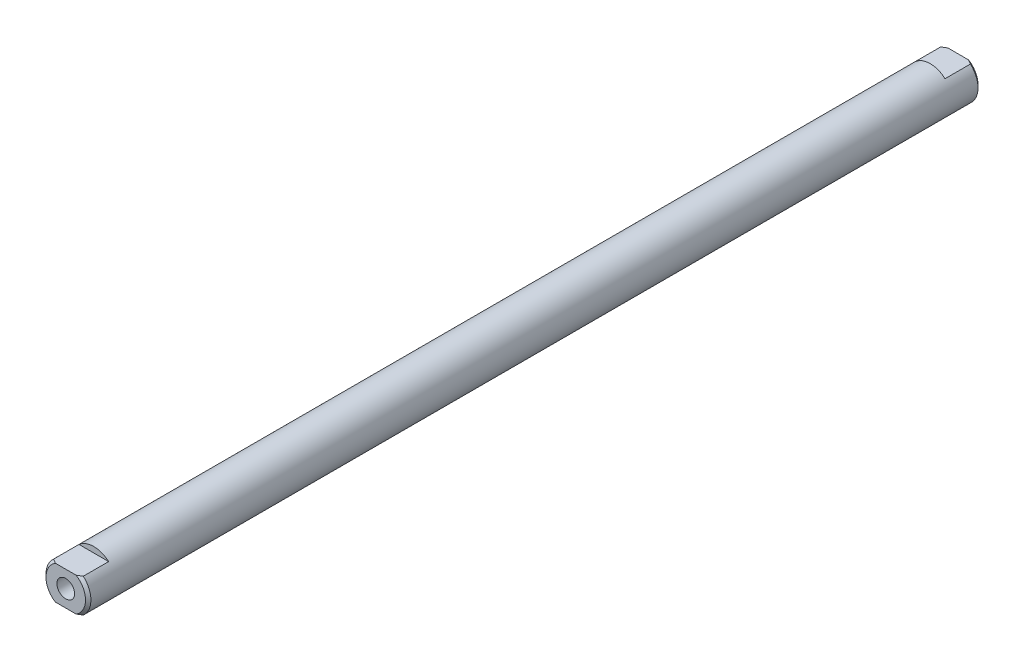
SolidWorks part; units mm, degrees
material "AISI Type A2 Tool Steel"
ref_plane "Front Plane" through (0, 0, 0) normal (0, 0, 1) x (1, 0, 0)
ref_plane "Top Plane" through (0, 0, 0) normal (0, 1, 0) x (1, 0, 0)
ref_plane "Right Plane" through (0, 0, 0) normal (1, 0, 0) x (0, 0, -1)
sketch "Sketch1" plane through (0, 0, 0) normal (0, 0, 1) x (1, 0, 0)
  circle A0 centre (0, 0) radius 3.175
  dimension "D1" = 6.35
extrude "Boss-Extrude1" add sketch "Sketch1" along normal mid plane 126.238
hole_wizard "M3x0.5 Tapped Hole1" positions "Sketch2" profile "Sketch4" tap size "M3x0.5" standard "ANSI Metric"
sketch "Sketch2" plane through (0, 0, 63.119) normal (0, 0, 1) x (1, 0, 0)
  point P0 (0, 0)
sketch "Sketch4" plane through (0, 0, 63.119) normal (1, 0, 0) x (0, -1, 0)
  line L0 (0, 0) -> (0, 8.2441)
  line L1 (0, 8.2441) -> (1.25, 7.493)
  line L2 (1.25, 7.493) -> (1.25, 0)
  line L5 (1.25, 0) -> (0, 0)
  line L10 (0, 8.2441) -> (-1.25, 7.493) construction
  line L11 (0, -6.35) -> (0, 107.95) construction
  dimension "Tap Drill Dia." = 2.5
  dimension "Tap Drill Depth" = 7.493
  dimension "Drill Angle" = 118
cosmetic thread "Hole Thread1" parameters "D1"=5.9944, "D2"=3
chamfer "Chamfer1" distance 0.381 angle 45
mirror "Mirror1" about plane through (0, 0, 0) normal (0, 0, 1) of "M3x0.5 Tapped Hole1"
sketch "Sketch5" plane through (0, 0, 63.119) normal (0, 0, 1) x (1, 0, 0)
  line L0 (-2.1001, 2.3813) -> (2.1001, 2.3813)
  line L1 (-5.3163, 0) -> (7.4474, 0) construction
  line L2 (-2.1001, -2.3813) -> (2.1001, -2.3813)
  circle A0 centre (0, 0) radius 3.175 construction
  arc A1 (2.1001, 2.3813) -> (-2.1001, 2.3813) centre (0, 0) ccw
  arc A2 (-2.1001, -2.3813) -> (2.1001, -2.3813) centre (0, 0) ccw
  dimension "D1" = 4.7625
extrude "Cut-Extrude1" cut sketch "Sketch5" against normal blind 3.9688
mirror "Mirror2" about plane through (0, 0, 0) normal (0, 0, 1) of "Cut-Extrude1"
